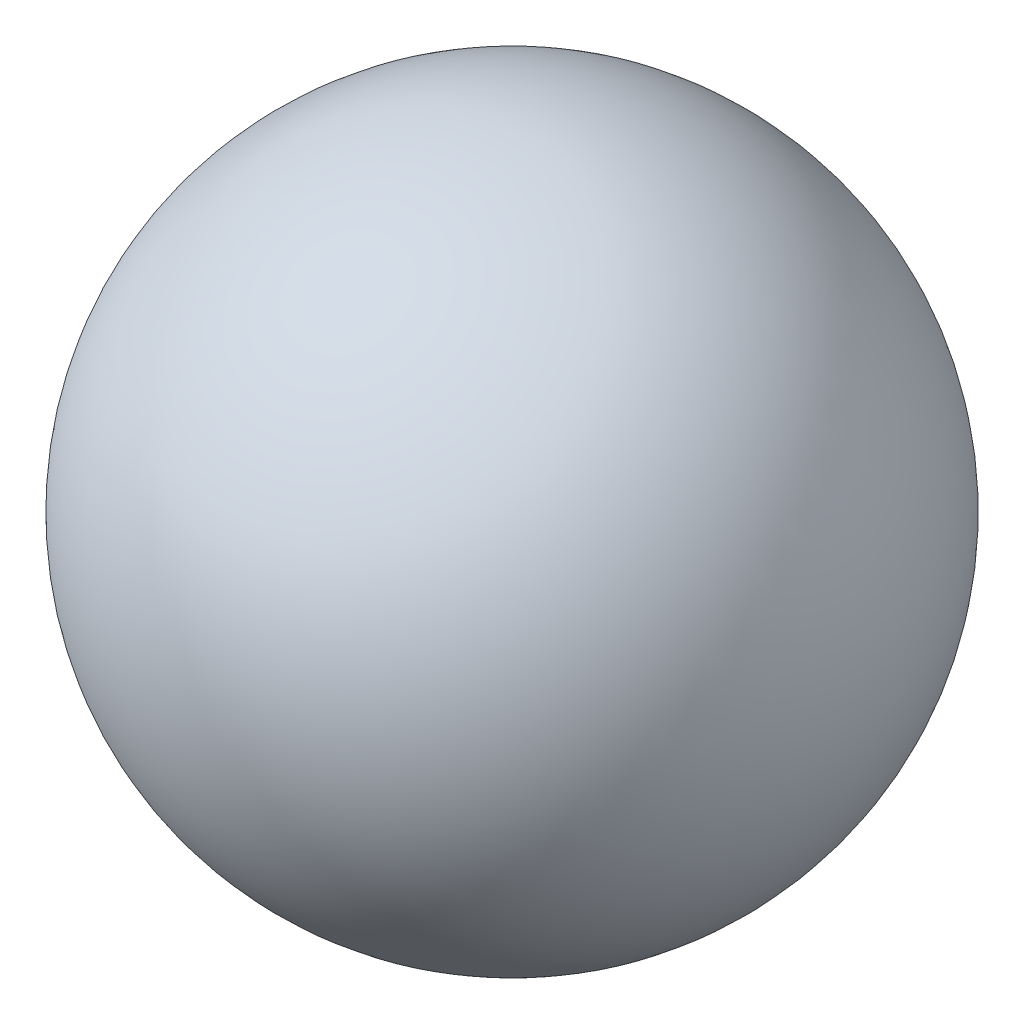
SolidWorks part; units mm, degrees
ref_plane "前视基准面" through (0, 0, 0) normal (0, 0, 1) x (1, 0, 0)
ref_plane "上视基准面" through (0, 0, 0) normal (0, 1, 0) x (1, 0, 0)
ref_plane "右视基准面" through (0, 0, 0) normal (1, 0, 0) x (0, 0, -1)
sketch "草图1" plane through (0, 0, 0) normal (0, 0, 1) x (1, 0, 0)
  line L1 (0, 29.6071) -> (0, -31.1334) construction
  line L2 (0, -20) -> (0, 20)
  arc A0 (0, -20) -> (0, 20) centre (0, 0) cw
  dimension "D1" = 20
revolve "旋转1" add sketch "草图1" angle 360 about L1
